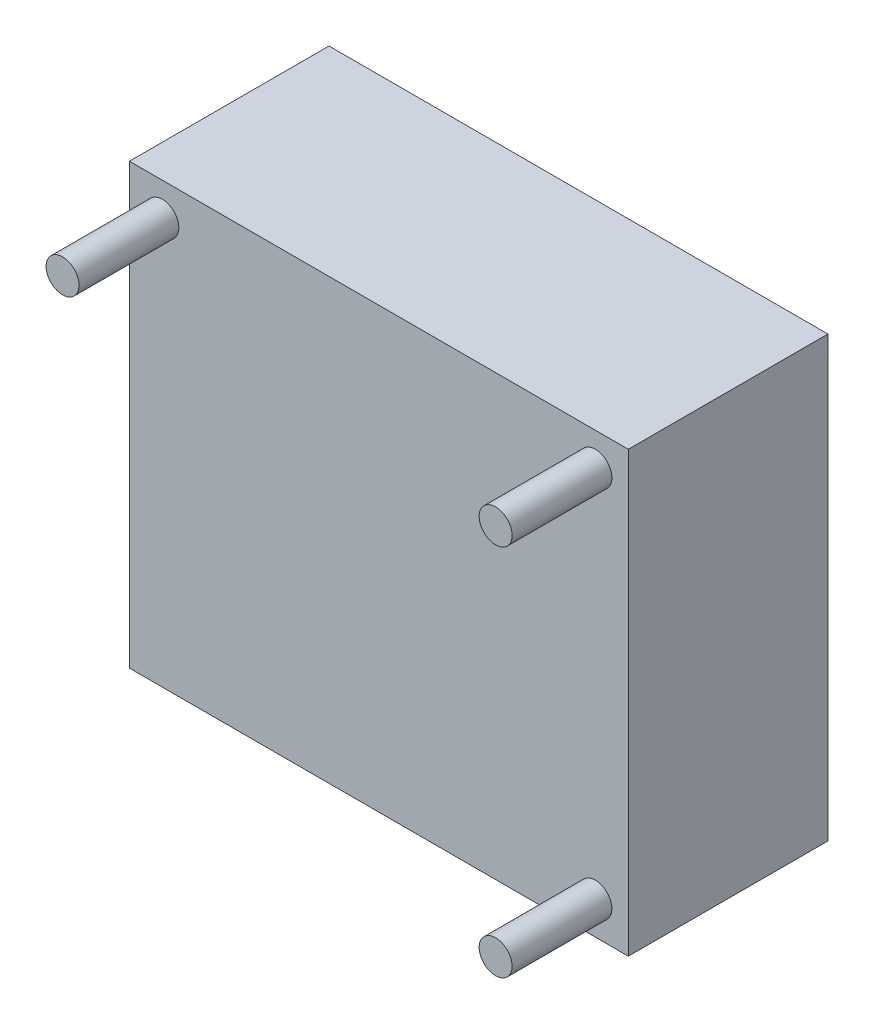
SolidWorks part; units mm, degrees
ref_plane "Front Plane" through (0, 0, 0) normal (0, 0, 1) x (1, 0, 0)
ref_plane "Top Plane" through (0, 0, 0) normal (0, 1, 0) x (1, 0, 0)
ref_plane "Right Plane" through (0, 0, 0) normal (1, 0, 0) x (0, 0, -1)
sketch "Sketch1" plane through (0, 0, 0) normal (0, 0, 1) x (1, 0, 0)
  line L0 (0, 22) -> (50, 22) construction
  line L1 (0, 0) -> (50, 0)
  line L2 (0, 0) -> (0, 44)
  line L3 (0, 44) -> (50, 44)
  line L4 (50, 0) -> (50, 44)
  line L5 (25, 44) -> (25, 0) construction
  circle A0 centre (46.7, 40.7) radius 1.65
  circle A1 centre (3.3, 40.7) radius 1.65
  circle A2 centre (46.7, 3.3) radius 1.65
  point P11 (25, 22)
  dimension "D3" = 3.3
  dimension "D1" = 44
  dimension "D2" = 50
  dimension "D4" = 3.3
  dimension "D5" = 3.3
extrude "Boss-Extrude1" add sketch "Sketch1" along normal blind 20
sketch "Sketch3" plane through (0, 0, 0) normal (0, 0, -1) x (-1, 0, 0)
  circle A0 centre (-46.7, 40.7) radius 1.65 construction
  circle A1 centre (-46.7, 3.3) radius 1.65 construction
  circle A2 centre (-3.3, 40.7) radius 1.65 construction
  circle A3 centre (-46.7, 40.7) radius 1.65
  circle A4 centre (-46.7, 3.3) radius 1.65
  circle A5 centre (-3.3, 40.7) radius 1.65
extrude "Boss-Extrude2" add sketch "Sketch3" against normal blind 30 separate body
